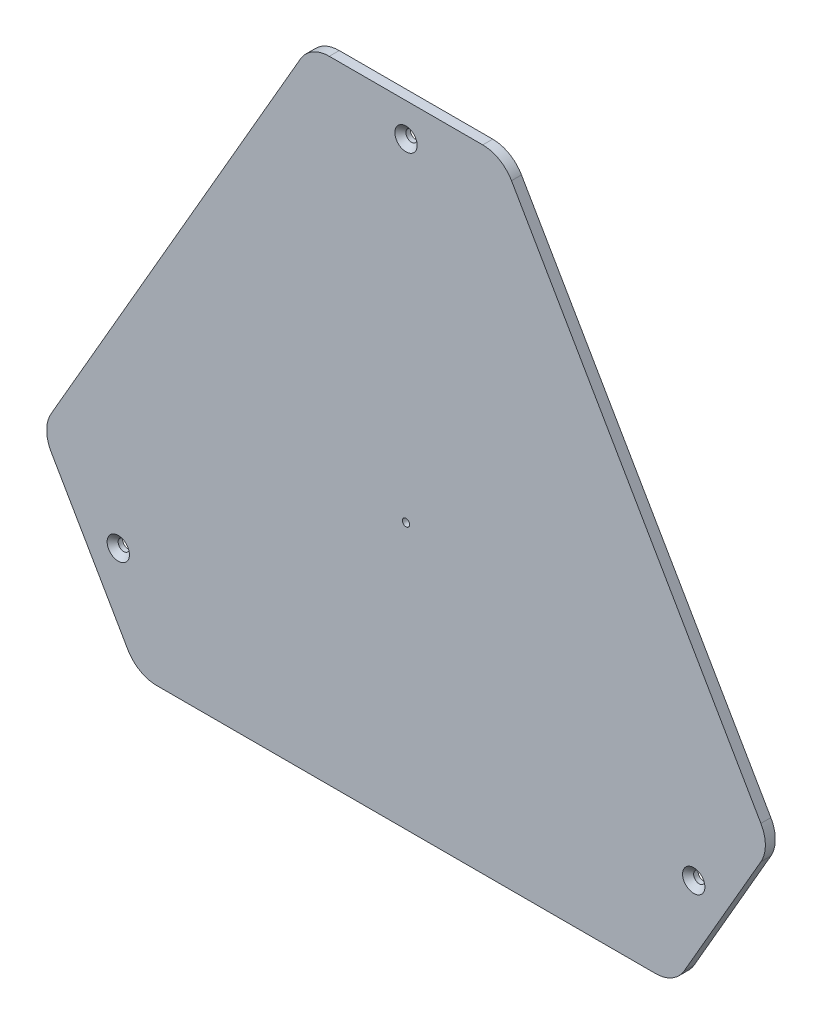
SolidWorks part; units mm, degrees
material "Alliage 1060"
ref_plane "Plan de face" through (0, 0, 0) normal (0, 0, 1) x (1, 0, 0)
ref_plane "Plan de dessus" through (0, 0, 0) normal (0, 1, 0) x (1, 0, 0)
ref_plane "Plan de droite" through (0, 0, 0) normal (1, 0, 0) x (0, 0, -1)
sketch "Esquisse1" plane through (0, 0, 0) normal (0, 0, 1) x (1, 0, 0)
  line L0 (23.094, 110) -> (-23.094, 110)
  line L3 (-31.7543, 105) -> (-106.8098, -25)
  line L4 (0, 0) -> (-69.282, 40) construction
  line L9 (0, 0) -> (0, 110) construction
  line L10 (83.7158, -75) -> (106.8098, -35)
  line L11 (106.8098, -25) -> (31.7543, 105)
  line L12 (0, 0) -> (69.282, 40) construction
  line L13 (0, 0) -> (95.2628, -55) construction
  line L14 (-106.8098, -35) -> (-83.7158, -75)
  line L15 (-75.0555, -80) -> (75.0555, -80)
  line L16 (0, 0) -> (0, -80) construction
  line L17 (0, 0) -> (-95.2628, -55) construction
  circle A0 centre (0, 0) radius 80 construction
  arc A1 (-106.8098, -25) -> (-106.8098, -35) centre (-98.1495, -30) ccw
  arc A2 (-83.7158, -75) -> (-75.0555, -80) centre (-75.0555, -70) ccw
  arc A3 (75.0555, -80) -> (83.7158, -75) centre (75.0555, -70) ccw
  arc A4 (106.8098, -35) -> (106.8098, -25) centre (98.1495, -30) ccw
  arc A5 (31.7543, 105) -> (23.094, 110) centre (23.094, 100) ccw
  arc A6 (-23.094, 110) -> (-31.7543, 105) centre (-23.094, 100) ccw
  point P25 (0, 0)
  dimension "D2" = 110
  dimension "D1" = 160
  dimension "D7" = 10
  dimension "D3" = 120
  dimension "D5" = 60
  dimension "D6" = 80
  dimension "D4" = 3
extrude "Boss.-Extru.1" add sketch "Esquisse1" along normal blind 3
hole_wizard "Fraisage pour vis à tête fraisée à 6 pans creux M31" positions "Esquisse3" profile "Esquisse2" countersink size "M3" standard "ISO"
sketch "Esquisse3" plane through (0, 0, 3) normal (0, 0, 1) x (1, 0, 0)
  line L0 (-86.6025, -50) -> (0, 0) construction
  line L1 (0, 0) -> (86.6025, -50) construction
  line L3 (0, 0) -> (0, 100) construction
  circle A0 centre (0, 0) radius 100 construction
  point P0 (0, 100)
  point P8 (86.6025, -50)
  point P9 (-86.6025, -50)
  dimension "D1" = 100
  dimension "D3" = 120
  dimension "D2" = 3
sketch "Esquisse2" plane through (0, 100, 3) normal (1, 0, 0) x (0, -1, 0)
  line L0 (0, 0) -> (0, 30.9815)
  line L1 (0, 30.9815) -> (1.7, 30)
  line L2 (1.7, 30) -> (1.7, 1.66)
  line L3 (1.7, 1.66) -> (3.36, 0)
  line L5 (3.36, 0) -> (0, 0)
  line L6 (-1.7, 1.66) -> (-3.36, 0) construction
  line L10 (0, 30.9815) -> (-1.7, 30) construction
  line L11 (0, -6.35) -> (0, 107.95) construction
  dimension "Diamètre du perçage" = 3.4
  dimension "Profondeur du perçage" = 30
  dimension "Diamètre du fraisage entrant" = 6.72
  dimension "Angle du fraisage entrant" = 90
  dimension "Angle de pointe" = 120
sketch "Esquisse4" plane through (0, 0, 3) normal (0, 0, 1) x (1, 0, 0)
  line L0 (-86.6025, -50) -> (0, 0) construction
  line L1 (0, 0) -> (0, 100) construction
  circle A0 centre (0, 0) radius 1.1
  dimension "D2" = 2.2
  dimension "D1" = 100
extrude "Enlèv. mat.-Extru.1" cut sketch "Esquisse4" against normal blind 10
sketch "Esquisse5" plane through (0, 0, 0) normal (0, 0, 1) x (1, 0, 0)
  line L0 (17.3205, 110) -> (103.923, -40) construction
  line L1 (106.8098, -25) -> (31.7543, 105) construction
  line L2 (83.7158, -75) -> (106.8098, -35) construction
  line L3 (23.094, 110) -> (-23.094, 110) construction
  text T0 "eMotion Tech\r\nCC BY-NC-SA"
  dimension "D1" = 10
extrude "Enlèv. mat.-Extru.5" cut sketch "Esquisse5" along normal blind 0.5
